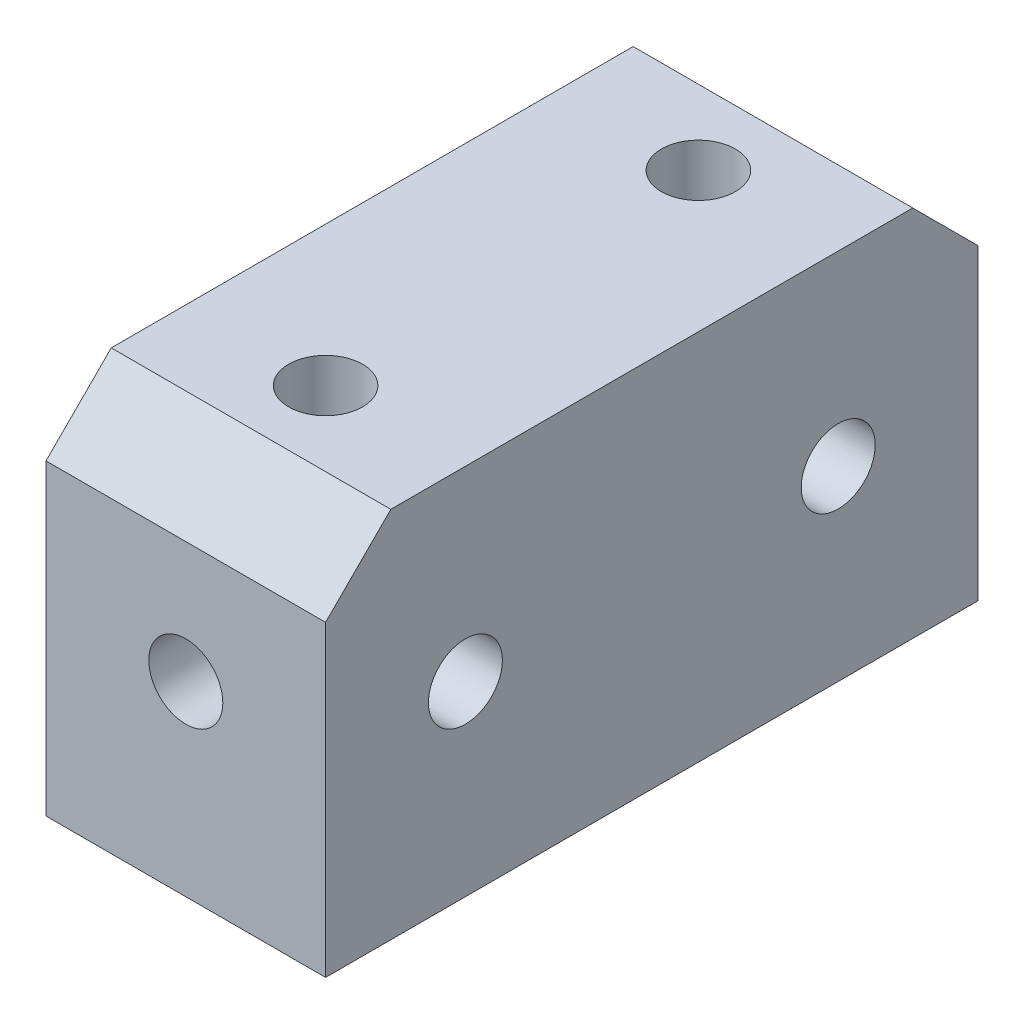
SolidWorks part; units mm, degrees
material "ABS"
ref_plane "Plano frontal" through (0, 0, 0) normal (0, 0, 1) x (1, 0, 0)
ref_plane "Plano superior" through (0, 0, 0) normal (0, 1, 0) x (1, 0, 0)
ref_plane "Plano direito" through (0, 0, 0) normal (1, 0, 0) x (0, 0, -1)
sketch "Esboço1" plane through (0, 0, 0) normal (1, 0, 0) x (0, 0, -1)
  line L0 (-35, 0) -> (-20, 0) construction
  line L1 (35, 20) -> (-35, 20)
  line L2 (35, 20) -> (35, -20)
  line L3 (35, -20) -> (-35, -20)
  line L4 (-35, 20) -> (-35, -20)
  line L5 (35, 20) -> (-35, -20) construction
  line L6 (35, -20) -> (-35, 20) construction
  line L7 (-20, 0) -> (20, 0) construction
  line L8 (20, 0) -> (35, 0) construction
  circle A0 centre (-20, 0) radius 3.97
  circle A1 centre (20, 0) radius 3.97
  point P0 (0, 0)
  dimension "D4" = 7.94
  dimension "D1" = 40
  dimension "D2" = 70
  dimension "D3" = 40
extrude "Ressalto-extrusão1" add sketch "Esboço1" along normal mid plane 30
sketch "Esboço3" plane through (0, 0, 35) normal (0, 0, 1) x (1, 0, 0)
  circle A0 centre (0, 0) radius 3.97
  dimension "D1" = 7.94
extrude "Corte-extrusão2" cut sketch "Esboço3" against normal blind 15
sketch "Esboço4" plane through (0, 20, 0) normal (0, 1, 0) x (1, 0, 0)
  line L0 (0, -35) -> (0, -20) construction
  line L1 (15, -35) -> (-15, -35) construction
  line L2 (0, -20) -> (0, 20) construction
  line L3 (0, 20) -> (0, 35) construction
  line L4 (15, 35) -> (-15, 35) construction
  circle A0 centre (0, 20) radius 3.97
  circle A1 centre (0, -20) radius 3.97
  dimension "D2" = 7.94
  dimension "D1" = 40
extrude "Corte-extrusão3" cut sketch "Esboço4" against normal blind 20
chamfer "Chanfro2" distance 7 angle 45 2 edges at (0, 20, -35) (0, 20, 35)
